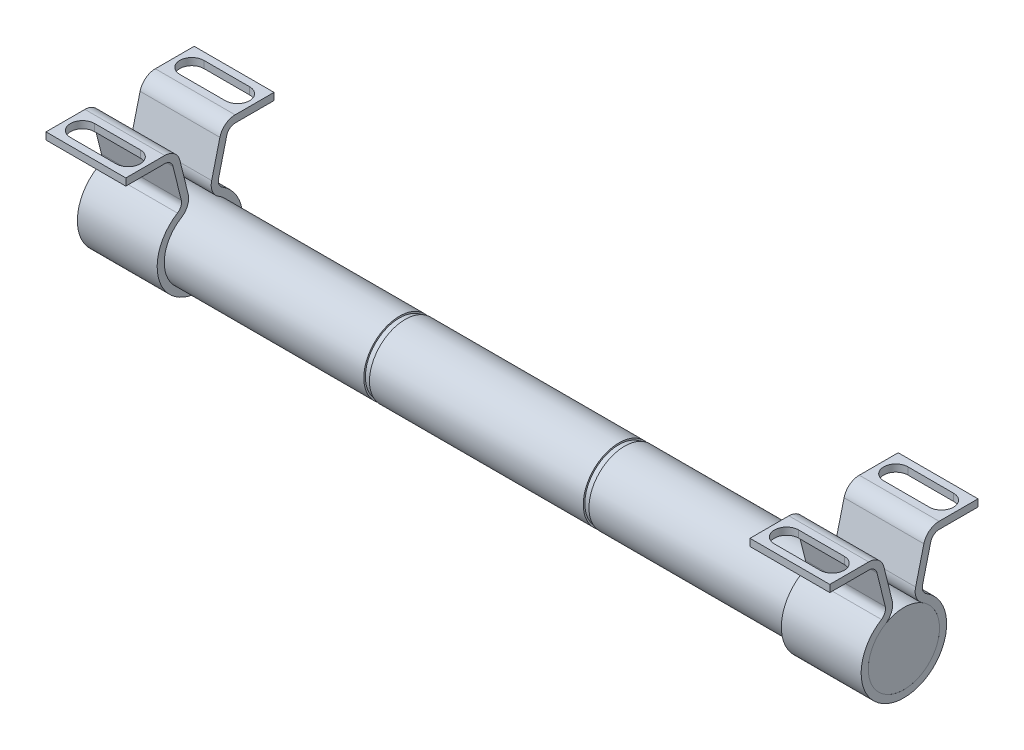
SolidWorks part; units mm, degrees
material "Plain Carbon Steel"
ref_plane "Front Plane" through (0, 0, 0) normal (0, 0, 1) x (1, 0, 0)
ref_plane "Top Plane" through (0, 0, 0) normal (0, 1, 0) x (1, 0, 0)
ref_plane "Right Plane" through (0, 0, 0) normal (1, 0, 0) x (0, 0, -1)
sketch "Sketch1" plane through (0, 0, 0) normal (1, 0, 0) x (0, 0, -1)
  circle A0 centre (0, 0) radius 12.5
  dimension "D2" = 25
extrude "Boss-Extrude1" add sketch "Sketch1" along normal mid plane 275
sketch "Sketch2" plane through (137.5, 0, 0) normal (1, 0, 0) x (0, 0, -1)
  line L0 (0, 0) -> (0, 32.5) construction
  line L1 (8.0433, 32.5) -> (-8.0433, 32.5) construction
  line L2 (-12.3481, 32.5) -> (-26, 32.5)
  line L3 (-26, 32.5) -> (-26, 30)
  line L4 (-26, 30) -> (-12.3481, 30)
  line L5 (-9.4359, 27.7207) -> (-6.5443, 16.0366)
  line L6 (-7.0091, 28.3213) -> (-4.1175, 16.6372)
  line L7 (7.0091, 28.3213) -> (4.1175, 16.6372)
  line L8 (9.4359, 27.7207) -> (6.5443, 16.0366)
  line L9 (26, 30) -> (12.3481, 30)
  line L10 (26, 32.5) -> (26, 30)
  line L11 (12.3481, 32.5) -> (26, 32.5)
  arc A0 (-7.8803, 12.7632) -> (7.8803, 12.7632) centre (0, 0) ccw
  circle A1 centre (0, 0) radius 12.5
  arc A2 (-6.5669, 10.636) -> (6.5669, 10.636) centre (0, 0) ccw
  circle A3 centre (0, 0) radius 15 construction
  circle A4 centre (0, 0) radius 12.5 construction
  arc A5 (6.5443, 16.0366) -> (7.8803, 12.7632) centre (9.4564, 15.3159) ccw
  arc A6 (9.4359, 27.7207) -> (12.3481, 30) centre (12.3481, 27) cw
  arc A7 (-12.3481, 30) -> (-9.4359, 27.7207) centre (-12.3481, 27) cw
  arc A8 (-6.5443, 16.0366) -> (-7.8803, 12.7632) centre (-9.4564, 15.3159) cw
  arc A9 (-12.3481, 32.5) -> (-7.0091, 28.3213) centre (-12.3481, 27) cw
  arc A10 (7.0091, 28.3213) -> (12.3481, 32.5) centre (12.3481, 27) cw
  arc A11 (4.1175, 16.6372) -> (6.5669, 10.636) centre (9.4564, 15.3159) ccw
  arc A12 (-4.1175, 16.6372) -> (-6.5669, 10.636) centre (-9.4564, 15.3159) cw
  point P20 (5.98, 13.7565)
  point P23 (10, 30)
  point P26 (-10, 30)
  point P29 (-5.98, 13.7565)
  point P38 (3.003, 12.1339)
  point P41 (-3.003, 12.1339)
  dimension "D7" = 20
  dimension "D8" = 3
  dimension "D9" = 5.5
  dimension "D2" = 2.5
  dimension "D3" = 2.5
  dimension "D5" = 26
  dimension "D6" = 16
  dimension "D1" = 0
  dimension "D4" = 2.5
extrude "Boss-Extrude2" add sketch "Sketch2" against normal blind 25 and the other way blind 3 from offset 3 separate body offset against normal yes
sketch "Sketch8" plane through (0, 32.5, 0) normal (0, 1, 0) x (1, 0, 0)
  line L0 (123.5, 26) -> (123.5, 12.3481) construction
  line L1 (109.5, 26) -> (137.5, 26) construction
  line L2 (109.5, 12.3481) -> (137.5, 12.3481) construction
  line L3 (109.5, 19.174) -> (137.5, 19.174) construction
  line L4 (109.5, 26) -> (109.5, 12.3481) construction
  line L5 (137.5, 26) -> (137.5, 12.3481) construction
  line L6 (115.5, 19.174) -> (131.5, 19.174) construction
  line L7 (115.5, 23.424) -> (131.5, 23.424)
  line L8 (115.5, 14.924) -> (131.5, 14.924)
  arc A1 (115.5, 23.424) -> (115.5, 14.924) centre (115.5, 19.174) ccw
  arc A2 (131.5, 14.924) -> (131.5, 23.424) centre (131.5, 19.174) ccw
  point P14 (123.5, 19.174)
  dimension "D1" = 8.5
  dimension "D2" = 6
extrude "Cut-Extrude3" cut sketch "Sketch8" against normal blind 9
mirror "Mirror5" about plane through (0, 0, 0) normal (0, 0, 1) of "Cut-Extrude3"
mirror "Mirror1" about plane through (0, 0, 0) normal (1, 0, 0) of bodies 121 108
ref_plane "Plane1" through (138.5, 0, 0) normal (1, 0, 0) x (0, 0, -1)
ref_plane "Plane2" through (37.5, 0, 0) normal (1, 0, 0) x (0, 0, -1)
sketch "Sketch6" plane through (37.5, 0, 0) normal (1, 0, 0) x (0, 0, -1)
  circle A3 centre (0, 0) radius 13
  circle A4 centre (0, 0) radius 11.95
  dimension "D1" = 23.9
  dimension "D2" = 26
extrude "Cut-Extrude2" cut sketch "Sketch6" along normal blind 2
mirror "Mirror4" about plane through (0, 0, 0) normal (1, 0, 0) of "Cut-Extrude2"
